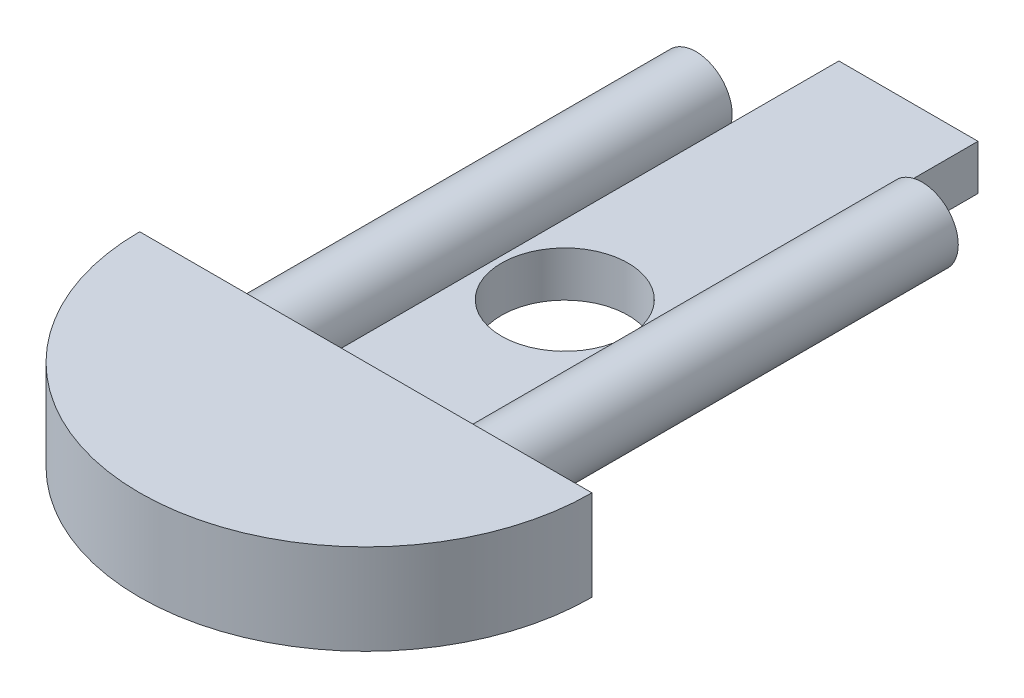
SolidWorks part; units mm, degrees
ref_plane "Front Plane" through (0, 0, 0) normal (0, 0, 1) x (1, 0, 0)
ref_plane "Top Plane" through (0, 0, 0) normal (0, 1, 0) x (1, 0, 0)
ref_plane "Right Plane" through (0, 0, 0) normal (1, 0, 0) x (0, 0, -1)
sketch "Sketch2" plane through (0, 0, 0) normal (0, 0, 1) x (1, 0, 0)
  line L1 (0, 0) -> (31.75, 0)
  line L2 (0, 0) -> (0, 12.7)
  line L3 (0, 12.7) -> (31.75, 12.7)
  line L4 (31.75, 0) -> (31.75, 12.7)
  line L5 (0, 0) -> (31.75, 12.7) construction
  line L6 (0, 12.7) -> (31.75, 0) construction
  point P4 (15.875, 6.35)
revolve "Revolve1" add sketch "Sketch2" angle 180 about L4
sketch "Sketch3" plane through (0, 0, 0) normal (0, 0, -1) x (-1, 0, 0)
  line L0 (-31.75, 12.7) -> (-63.5, 12.7) construction
  line L1 (0, 12.7) -> (-63.5, 12.7) construction
  line L2 (-31.75, 12.7) -> (0, 12.7) construction
  circle A0 centre (-47.625, 6.35) radius 5.08
  circle A1 centre (-15.875, 6.35) radius 5.08
extrude "Boss-Extrude1" add sketch "Sketch3" along normal blind 62.23
sketch "Sketch4" plane through (0, 0, 0) normal (0, 0, -1) x (-1, 0, 0)
  line L0 (-42.545, 6.35) -> (-41.5036, 6.35) construction
  line L1 (-20.955, 6.35) -> (-21.971, 6.35) construction
  line L2 (-63.5, 0) -> (0, 0) construction
  line L3 (-41.5036, 0) -> (-21.971, 0)
  line L4 (-41.5036, 0) -> (-41.5036, 6.35)
  line L5 (-41.5036, 6.35) -> (-21.971, 6.35)
  line L6 (-21.971, 0) -> (-21.971, 6.35)
  line L7 (-41.5036, 0) -> (-21.971, 6.35) construction
  line L8 (-41.5036, 6.35) -> (-21.971, 0) construction
  circle A2 centre (-47.625, 6.35) radius 5.08 construction
  circle A3 centre (-47.625, 6.35) radius 5.08 construction
  circle A4 centre (-15.875, 6.35) radius 5.08 construction
  point P16 (-31.7373, 3.175)
extrude "Boss-Extrude2" add sketch "Sketch4" along normal blind 76.2
sketch "Sketch5" plane through (0, 6.35, 0) normal (0, 1, 0) x (1, 0, 0)
  line L0 (31.75, 0) -> (31.75, 36.83) construction
  line L1 (0, 0) -> (63.5, 0) construction
  circle A1 centre (31.75, 27.94) radius 8.89
extrude "Cut-Extrude1" cut sketch "Sketch5" against normal blind 76.2
